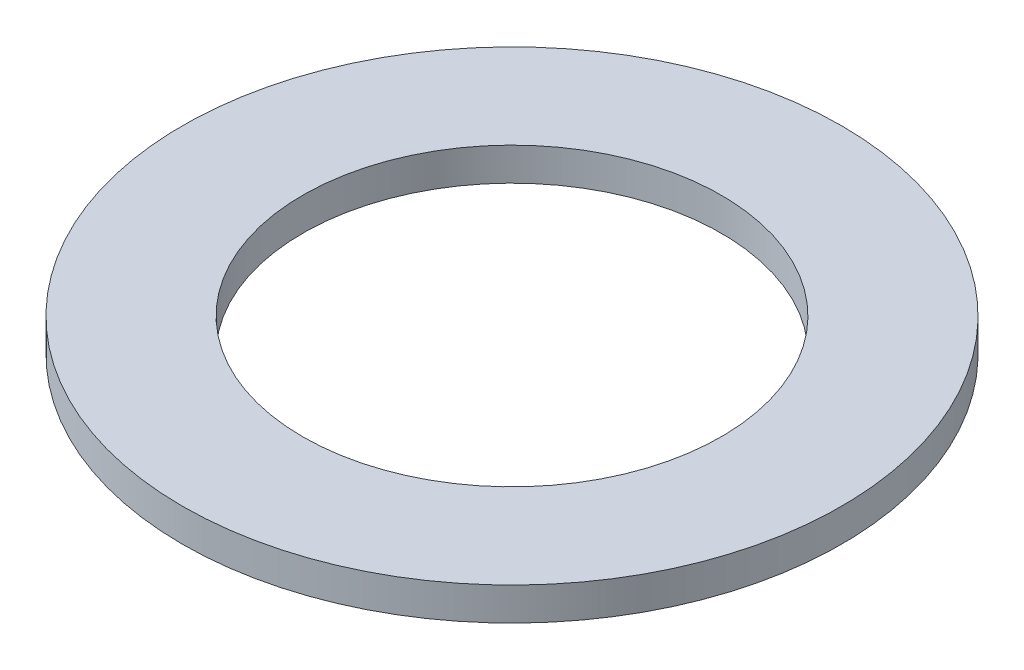
SolidWorks part; units mm, degrees
ref_plane "Alzado" through (0, 0, 0) normal (0, 0, 1) x (1, 0, 0)
ref_plane "Planta" through (0, 0, 0) normal (0, 1, 0) x (1, 0, 0)
ref_plane "Vista lateral" through (0, 0, 0) normal (1, 0, 0) x (0, 0, -1)
sketch "Croquis1" plane through (0, 0, 0) normal (0, 1, 0) x (1, 0, 0)
  circle A0 centre (0, 0) radius 19.05
  circle A1 centre (0, 0) radius 30
  dimension "D1" = 38.1
  dimension "D2" = 60
extrude "Saliente-Extruir1" add sketch "Croquis1" along normal blind 3
